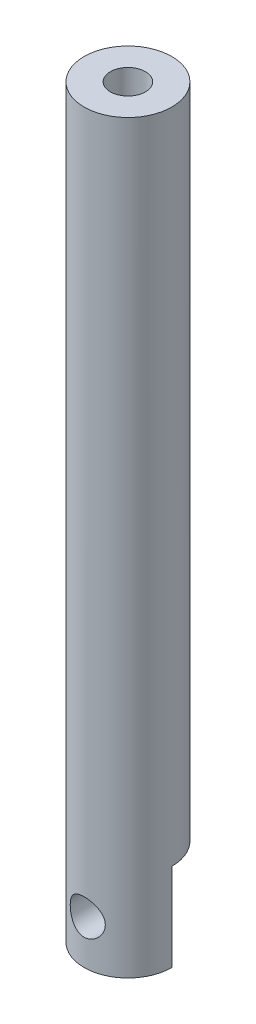
SolidWorks part; units mm, degrees
ref_plane "Front Plane" through (0, 0, 0) normal (0, 0, 1) x (1, 0, 0)
ref_plane "Top Plane" through (0, 0, 0) normal (0, 1, 0) x (1, 0, 0)
ref_plane "Right Plane" through (0, 0, 0) normal (1, 0, 0) x (0, 0, -1)
sketch "Sketch1" plane through (0, 0, 0) normal (0, 1, 0) x (1, 0, 0)
  circle A0 centre (0, 0) radius 5
extrude "Boss-Extrude1" add sketch "Sketch1" along normal blind 85
sketch "Sketch2" plane through (0, 85, 0) normal (0, 1, 0) x (1, 0, 0)
  circle A0 centre (0, 0) radius 2
extrude "Cut-Extrude1" cut sketch "Sketch2" against normal blind 15
sketch "Sketch3" plane through (0, 0, 0) normal (0, -1, 0) x (1, 0, 0)
  line L3 (5, 0) -> (-5, 0)
  circle A3 centre (0, 0) radius 5 construction
  arc A4 (5, 0) -> (-5, 0) centre (0, 0) cw
extrude "Cut-Extrude5" cut sketch "Sketch3" against normal blind 10
sketch "Sketch6" plane through (0, 0, 0) normal (0, 0, -1) x (-1, 0, 0)
  circle A0 centre (0, 5) radius 2
extrude "Cut-Extrude6" cut sketch "Sketch6" against normal through all
